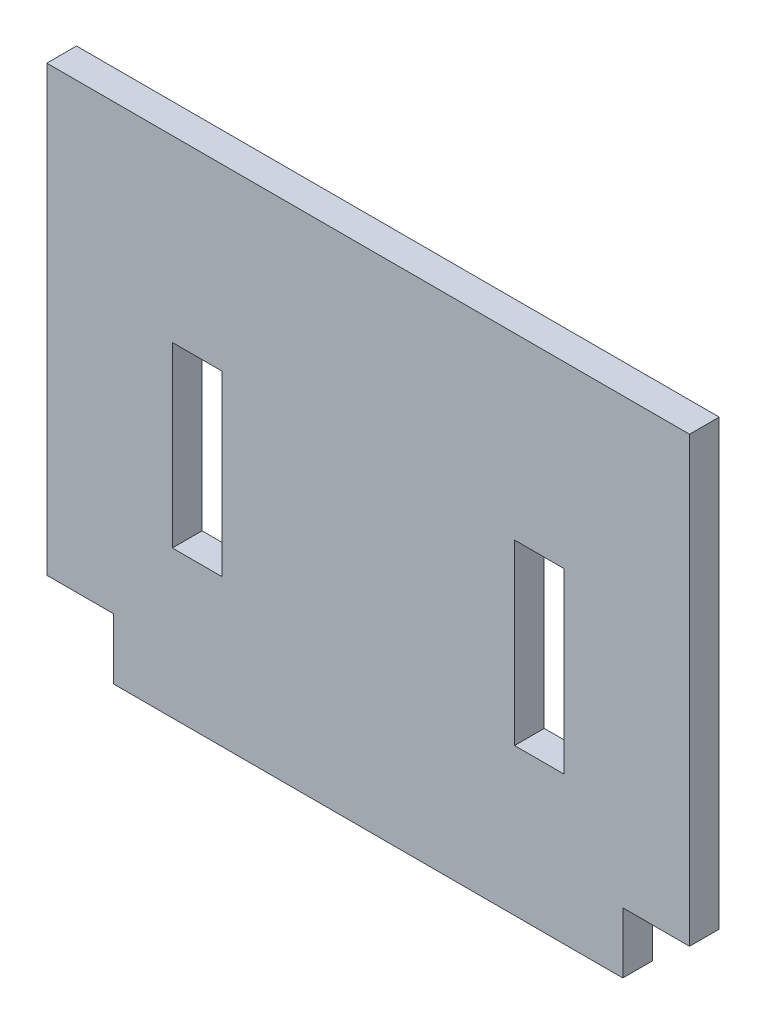
SolidWorks part; units mm, degrees
ref_plane "Front Plane" through (0, 0, 0) normal (0, 0, 1) x (1, 0, 0)
ref_plane "Top Plane" through (0, 0, 0) normal (0, 1, 0) x (1, 0, 0)
ref_plane "Right Plane" through (0, 0, 0) normal (1, 0, 0) x (0, 0, -1)
sketch "Sketch1" plane through (0, 0, 0) normal (0, 0, 1) x (1, 0, 0)
  line L1 (-776.7134, 983.7402) -> (-711.7134, 983.7402)
  line L2 (-776.7134, 983.7402) -> (-776.7134, 1034.7402)
  line L3 (-776.7134, 1034.7402) -> (-711.7134, 1034.7402)
  line L4 (-711.7134, 983.7402) -> (-711.7134, 1034.7402)
  dimension "D1" = 51
  dimension "D2" = 65
extrude "Boss-Extrude1" add sketch "Sketch1" along normal blind 3
sketch "Sketch3" plane through (0, 0, 3) normal (0, 0, 1) x (1, 0, 0)
  line L1 (-776.7134, 983.7402) -> (-769.9634, 983.7402)
  line L2 (-776.7134, 983.7402) -> (-776.7134, 989.8902)
  line L3 (-776.7134, 989.8902) -> (-769.9634, 989.8902)
  line L4 (-769.9634, 983.7402) -> (-769.9634, 989.8902)
  line L5 (-711.7134, 983.7402) -> (-718.4634, 983.7402)
  line L6 (-711.7134, 983.7402) -> (-711.7134, 989.8902)
  line L7 (-711.7134, 989.8902) -> (-718.4634, 989.8902)
  line L8 (-718.4634, 983.7402) -> (-718.4634, 989.8902)
  dimension "D1" = 6.15
  dimension "D2" = 6.75
  dimension "D3" = 6.15
  dimension "D4" = 6.75
extrude "Cut-Extrude1" cut sketch "Sketch3" against normal through all
sketch "Sketch4" plane through (0, 0, 3) normal (0, 0, 1) x (1, 0, 0)
  line L0 (-776.7134, 1012.3152) -> (-711.7134, 1012.3152) construction
  line L1 (-776.7134, 1034.7402) -> (-776.7134, 989.8902) construction
  line L2 (-711.7134, 989.8902) -> (-711.7134, 1034.7402) construction
  line L3 (-761.5164, 1020.9941) -> (-726.9104, 1020.9941)
  line L4 (-711.7134, 1034.7402) -> (-776.7134, 1034.7402) construction
  line L5 (-744.2134, 1034.7402) -> (-744.2134, 983.7402) construction
  line L6 (-769.9634, 983.7402) -> (-718.4634, 983.7402) construction
  line L7 (-761.5164, 1020.9941) -> (-761.5164, 1007.6249)
  line L8 (-726.9104, 1020.9941) -> (-726.9104, 1007.6249)
  line L9 (-761.5164, 1007.6249) -> (-726.9104, 1007.6249)
  line L10 (-761.5164, 1020.9941) -> (-726.9104, 1007.6249) construction
  line L11 (-726.9104, 1020.9941) -> (-761.5164, 1007.6249) construction
  line L13 (-759.0164, 998.6249) -> (-764.0164, 998.6249)
  line L14 (-759.0164, 998.6249) -> (-759.0164, 1016.6249)
  line L15 (-759.0164, 1016.6249) -> (-764.0164, 1016.6249)
  line L16 (-764.0164, 998.6249) -> (-764.0164, 1016.6249)
  line L17 (-759.0164, 998.6249) -> (-764.0164, 1016.6249) construction
  line L18 (-759.0164, 1016.6249) -> (-764.0164, 998.6249) construction
  line L19 (-729.4104, 998.6249) -> (-724.4104, 998.6249)
  line L20 (-729.4104, 998.6249) -> (-729.4104, 1016.6249)
  line L21 (-729.4104, 1016.6249) -> (-724.4104, 1016.6249)
  line L22 (-724.4104, 998.6249) -> (-724.4104, 1016.6249)
  line L23 (-729.4104, 998.6249) -> (-724.4104, 1016.6249) construction
  line L24 (-729.4104, 1016.6249) -> (-724.4104, 998.6249) construction
  point P13 (-744.2134, 1014.3095)
  point P25 (0, 0)
  dimension "D1" = 18
  dimension "D2" = 5
  dimension "D3" = 18
  dimension "D4" = 5
extrude "Cut-Extrude2" cut sketch "Sketch4" against normal through all contours L16 L13 L14 L9 L7 L15 | L14 L15 L7 L9 | L19 L22 L21 L8 L9 L20 | L21 L20 L9 L8
